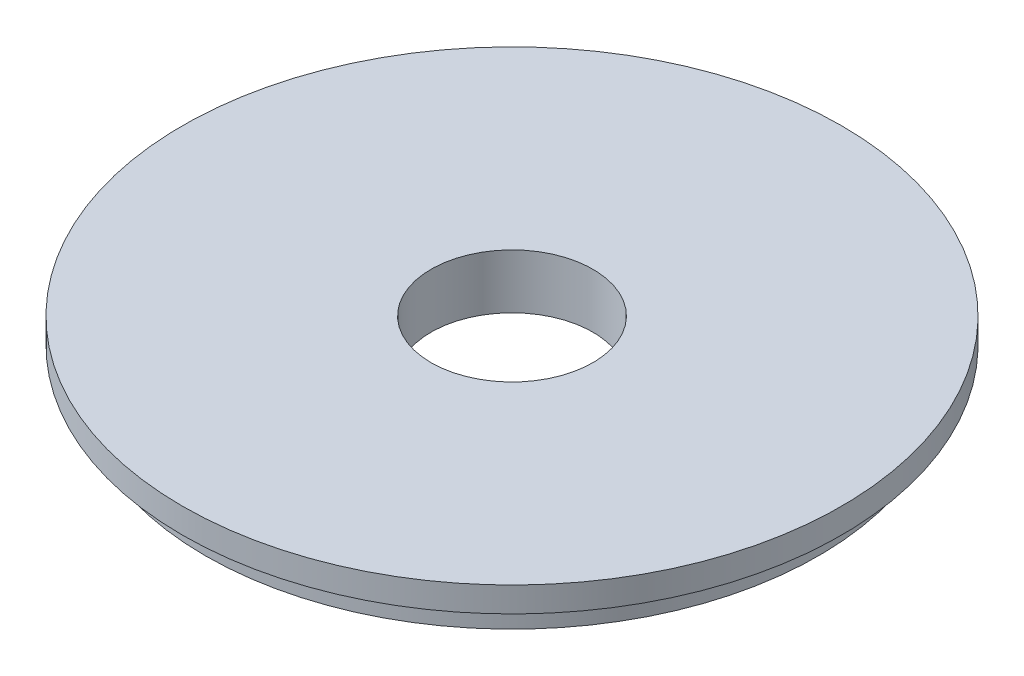
SolidWorks part; units mm, degrees
material "Phenolic Fiber Filled"
ref_plane "Front Plane" through (0, 0, 0) normal (0, 0, 1) x (1, 0, 0)
ref_plane "Top Plane" through (0, 0, 0) normal (0, 1, 0) x (1, 0, 0)
ref_plane "Right Plane" through (0, 0, 0) normal (1, 0, 0) x (0, 0, -1)
sketch "Sketch1" plane through (0, 0, 0) normal (0, 0, 1) x (1, 0, 0)
  line L0 (0, 0) -> (-11.3157, 0) construction
  line L1 (-11.3157, 0) -> (-46.0756, 0)
  line L2 (-46.0756, 0) -> (-46.0756, -3.5052)
  line L3 (-46.0756, -3.5052) -> (-42.8625, -3.5052)
  line L4 (-42.8625, -3.5052) -> (-42.8625, -7.62)
  line L5 (-42.8625, -7.62) -> (-11.3157, -7.62)
  line L6 (-11.3157, -7.62) -> (-11.3157, 0)
  line L7 (0, 0) -> (0, -5.0066) construction
  dimension "D1" = 11.3157
  dimension "D2" = 46.0756
  dimension "D3" = 42.8625
  dimension "D4" = 7.62
  dimension "D5" = 3.5052
revolve "Revolve1" add sketch "Sketch1" angle 360 about L7
